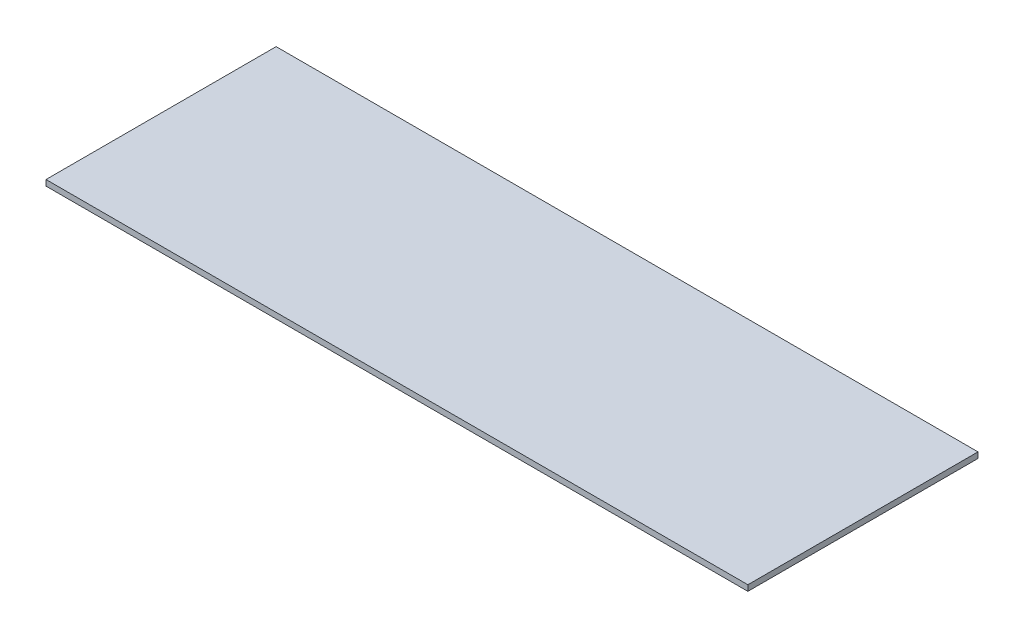
SolidWorks part; units mm, degrees
material "Oak"
ref_plane "Front Plane" through (0, 0, 0) normal (0, 0, 1) x (1, 0, 0)
ref_plane "Top Plane" through (0, 0, 0) normal (0, 1, 0) x (1, 0, 0)
ref_plane "Right Plane" through (0, 0, 0) normal (1, 0, 0) x (0, 0, -1)
sketch "Sketch1" plane through (0, 0, 0) normal (0, 1, 0) x (1, 0, 0)
  line L1 (-73.2022, 369.585) -> (1146.7978, 369.585)
  line L2 (-73.2022, 369.585) -> (-73.2022, -30.415)
  line L3 (-73.2022, -30.415) -> (1146.7978, -30.415)
  line L4 (1146.7978, 369.585) -> (1146.7978, -30.415)
  dimension "D1" = 1220
  dimension "D2" = 400
extrude "Boss-Extrude1" add sketch "Sketch1" along normal blind 10 contours L2 L3 L4 L1
